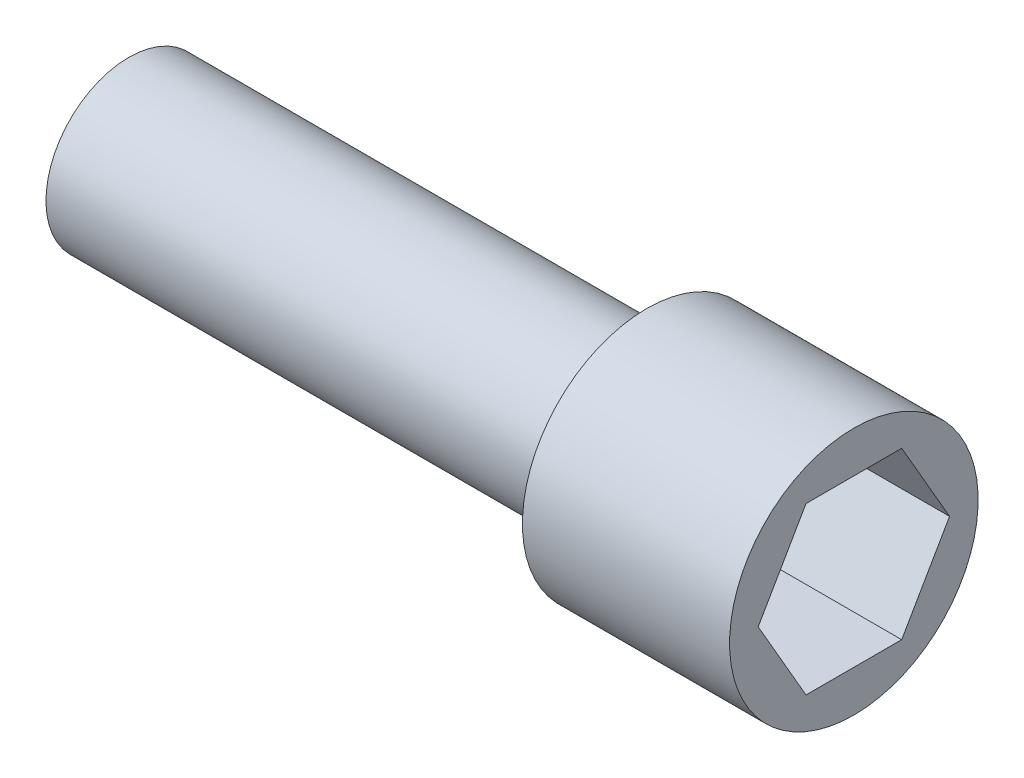
SolidWorks part; units mm, degrees
ref_plane "Front Plane" through (0, 0, 0) normal (0, 0, 1) x (1, 0, 0)
ref_plane "Top Plane" through (0, 0, 0) normal (0, 1, 0) x (1, 0, 0)
ref_plane "Right Plane" through (0, 0, 0) normal (1, 0, 0) x (0, 0, -1)
sketch "Sketch1" plane through (0, 0, 0) normal (0, 0, 1) x (1, 0, 0)
  line L0 (10, 0) -> (-25, 0)
  line L1 (-25, 0) -> (-25, 4)
  line L2 (-25, 4) -> (0, 4)
  line L3 (0, 4) -> (0, 6)
  line L4 (0, 6) -> (10, 6)
  line L5 (10, 6) -> (10, 0)
  point P7 (0, 0)
  point P8 (0, 0)
  point P9 (0, 0)
  dimension "D1" = 10
  dimension "D2" = 25
  dimension "D3" = 2
  dimension "D4" = 4
revolve "Revolve1" add sketch "Sketch1" angle 360 about L0
sketch "Sketch2" plane through (10, 0, 0) normal (1, 0, 0) x (0, 0, -1)
  line L1 (4.6188, 0) -> (2.3094, 4)
  line L2 (2.3094, 4) -> (-2.3094, 4)
  line L3 (-2.3094, 4) -> (-4.6188, 0)
  line L4 (-4.6188, 0) -> (-2.3094, -4)
  line L5 (-2.3094, -4) -> (2.3094, -4)
  line L6 (2.3094, -4) -> (4.6188, 0)
  circle A0 centre (0, 0) radius 4 construction
  point P1 (0, 0)
  point P10 (0, 0)
  dimension "D1" = 8
extrude "Cut-Extrude1" cut sketch "Sketch2" against normal blind 7
